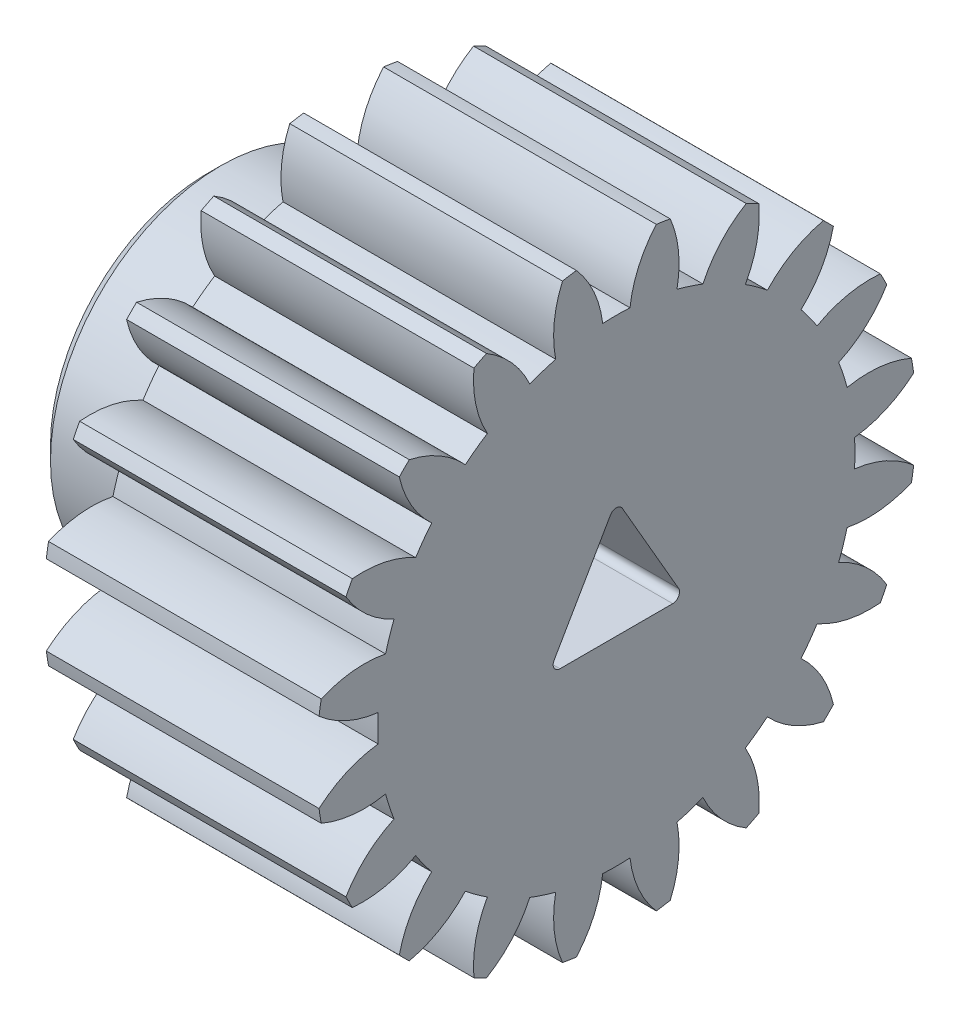
SolidWorks part; units mm, degrees
ref_plane "Front Plane" through (0, 0, 0) normal (0, 0, 1) x (1, 0, 0)
ref_plane "Top Plane" through (0, 0, 0) normal (0, 1, 0) x (1, 0, 0)
ref_plane "Right Plane" through (0, 0, 0) normal (1, 0, 0) x (0, 0, -1)
sketch "HoldingSke" plane through (0, 0, 0) normal (0, 1, 0) x (1, 0, 0)
  line L0 (0, 0) -> (0.9397, -0.342)
  line L1 (-15, 0) -> (100, 0) construction
  line L2 (0, 0) -> (-2.1039, 2.3779)
  line L3 (0, 0) -> (-11.863, 4.5341)
  line L4 (0, 0) -> (8.1152, 2.9537)
  line L5 (0, 0) -> (-46.8476, -17.4728)
  line L6 (0, 0) -> (-8.2896, -5.593)
  line L7 (-2.1039, 2.3779) -> (8.6586, 51.2059)
  line L8 (-76.2, 54.61) -> (-76.1, 54.61)
  line L9 (-71.009, 38.7566) -> (-53.1078, 45.2721)
  line L10 (-76.2, 71.12) -> (104.1128, 71.12)
  line L11 (0, 0) -> (-10, 0)
  line L12 (-76.2, 101.6) -> (-76.162, 101.6)
  line L13 (24.9733, 27.94) -> (52.9518, 28.4284)
  line L14 (24.9733, 27.94) -> (24.9743, 27.94)
  line L15 (24.9733, 27.94) -> (100.4006, 29.5858)
  line L16 (-63.627, -1) -> (-12.827, -1)
  circle A0 centre (0, 0) radius 0.4
  circle A1 centre (0, 0) radius 8.749
  circle A2 centre (0, 0) radius 37.5
  circle A3 centre (0, 0) radius 0.4
  dimension "MHD" = 17.498
  dimension "Hub_dia" = 75
  dimension "Bore" = 0.8
  dimension "MBD" = 0.8
  dimension "Num_teeth" = 20
  dimension "Pitch_radius" = 180.3128
  dimension "Pitch" = 1
  dimension "Width" = 10
  dimension "Overall_len" = 50
  dimension "Show_teeth" = 20
  dimension "Thickness" = 10
  dimension "OAL" = 50.0001
  dimension "T_dim" = 0.1
  dimension "Ap" = 20
  dimension "H" = 19.05
  dimension "Backlash" = 0.038
  dimension "Addendum_fac" = 1
  dimension "Dedendum_fac" = 1.25
  dimension "Clearance_fac" = 0.25
  dimension "Dedendum_add" = 0.001
  dimension "Module" = 1
sketch "BasProSke" plane through (0, 0, 0) normal (0, 1, 0) x (1, 0, 0)
  line L0 (-10, 0) -> (60, 0) construction
  line L1 (0, 0) -> (0, 11)
  line L2 (0, 0) -> (10, 0)
  line L3 (10, 0) -> (10, 11)
  line L4 (10, 11) -> (0, 11)
  dimension "Diameter" = 22
  dimension "Thickness" = 10
revolve "Base-Revolve" add sketch "BasProSke" angle 360 about L0
sketch "TooCutSke" plane through (0, 0, 0) normal (1, 0, 0) x (0, 0, -1)
  line L1 (0, 0) -> (0, 107) construction
  line L2 (0, 0) -> (-0.8511, 9.9637) construction
  line L3 (0, 0) -> (-3.1206, 19.7028) construction
  line L4 (-0.8511, 9.9637) -> (-1.5603, 9.8514) construction
  arc A0 (0.4999, 8.7347) -> (-0.4999, 8.7347) centre (0, 0) ccw
  arc A1 (1.4852, 10.9249) -> (-1.4852, 10.9249) centre (0, 0) ccw
  circle A2 centre (0, 0) radius 10 construction
  circle A3 centre (0, 0) radius 9.3969 construction
  arc A4 (-0.4999, 8.7347) -> (-1.4852, 10.9249) centre (-4.4722, 8.2645) ccw
  arc A5 (1.4852, 10.9249) -> (0.4999, 8.7347) centre (4.4722, 8.2645) ccw
  dimension "Root_dia" = 17.498
  dimension "Overcut_dia" = 22.0508
  dimension "Pitch_dia" = 20
  dimension "Base_dia" = 18.7939
  dimension "Flank_rad" = 4
  dimension "Half_ang" = 9
  dimension "Half_CT" = 0.7181
extrude "ToothCut" cut sketch "TooCutSke" along normal through all
fillet "Breaks" [suppressed] radius 0.02
fillet "RootFillets" [suppressed] radius 0.251
pattern_circular "TeethCuts" count 20 every 18 about axis through (-10, 0, 0) along (1, 0, 0) of "ToothCut", "RootFillets", "Breaks"
sketch "HubNeaOneSke" plane through (0, 0, 0) normal (-1, 0, 0) x (0, 0, 1)
  circle A0 centre (0, 0) radius 8.749
  dimension "Diameter" = 17.498
extrude "HubNearOne" [suppressed] add sketch "HubNeaOneSke" along normal blind 40.0001
sketch "HubNeaBotSke" plane through (0, 0, 0) normal (-1, 0, 0) x (0, 0, 1)
  circle A0 centre (0, 0) radius 8.749
  dimension "Diameter" = 17.498
extrude "HubNearBoth" [suppressed] add sketch "HubNeaBotSke" along normal blind 20
ref_plane "FarPln" through (10, 0, 0) normal (1, 0, 0) x (0, 0, -1)
sketch "HubFarSke" plane through (10, 0, 0) normal (1, 0, 0) x (0, 0, -1)
  circle A0 centre (0, 0) radius 8.749
  dimension "Diameter" = 17.498
extrude "HubFar" [suppressed] add sketch "HubFarSke" along normal blind 20
sketch "BorSke" plane through (0, 0, 0) normal (1, 0, 0) x (0, 0, -1)
  circle A0 centre (0, 0) radius 0.4
  dimension "Diameter" = 0.8
extrude "Bore" cut sketch "BorSke" along normal mid plane 100.0001
sketch "KeySke" plane through (0, 0, 0) normal (1, 0, 0) x (0, 0, -1)
  line L0 (-0.05, 0) -> (-0.05, 0.5)
  line L1 (-0.05, 0.5) -> (0.05, 0.5)
  line L2 (0.05, 0.5) -> (0.05, 0)
  line L3 (0, 0) -> (0, 34) construction
  line L4 (-0.05, 0) -> (0.05, 0)
  dimension "Offset" = 0.5
  dimension "Width" = 0.1
extrude "Keyway" [suppressed] cut sketch "KeySke" along normal mid plane 100.0001
pattern_circular "Keyway2" [suppressed] count 2 every 90 about axis through (-10, 0, 0) along (1, 0, 0)
sketch "Sketch1" plane through (0, 0, 0) normal (-1, 0, 0) x (0, 0, 1)
  circle A0 centre (0, 0) radius 6.25
  dimension "D1" = 12.5
extrude "Boss-Extrude1" add sketch "Sketch1" along normal blind 5
sketch "Sketch2" plane through (0, 0, 0) normal (1, 0, 0) x (0, 0, -1)
  line L0 (-2.5, -1.4434) -> (2.5, -1.4434)
  line L1 (2.5, -1.4434) -> (0, 2.8868)
  line L2 (0, 2.8868) -> (-2.5, -1.4434)
  line L3 (0, -1.4434) -> (0, 2.8868) construction
  line L4 (-2.5, -1.4434) -> (1.25, 0.7217) construction
  point P4 (0, 0)
  point P9 (1.25, 0.7217)
  dimension "D1" = 60
  dimension "D2" = 5
extrude "Cut-Extrude1" cut sketch "Sketch2" against normal through all and the other way through all
fillet "Fillet1" radius 0.5 1 edges at (0, 0, -6.25)
chamfer "Chamfer1" distance 0.5 angle 45 1 edges at (-5, 0, 6.25)
fillet "Fillet2" radius 0.25 3 edges at (2.5, -1.4434, 2.5) (2.5, -1.4434, -2.5) (2.5, 2.8868, 0)
ref_plane "Midplane" through (5, 0, 0) normal (-1, 0, 0) x (0, 0, 1)
sketch "Sketch3" plane through (5, 0, 0) normal (-1, 0, 0) x (0, 0, 1)
  line L0 (0, 0) -> (0, 10)
  circle A0 centre (0, 0) radius 10
  dimension "D1" = 20
